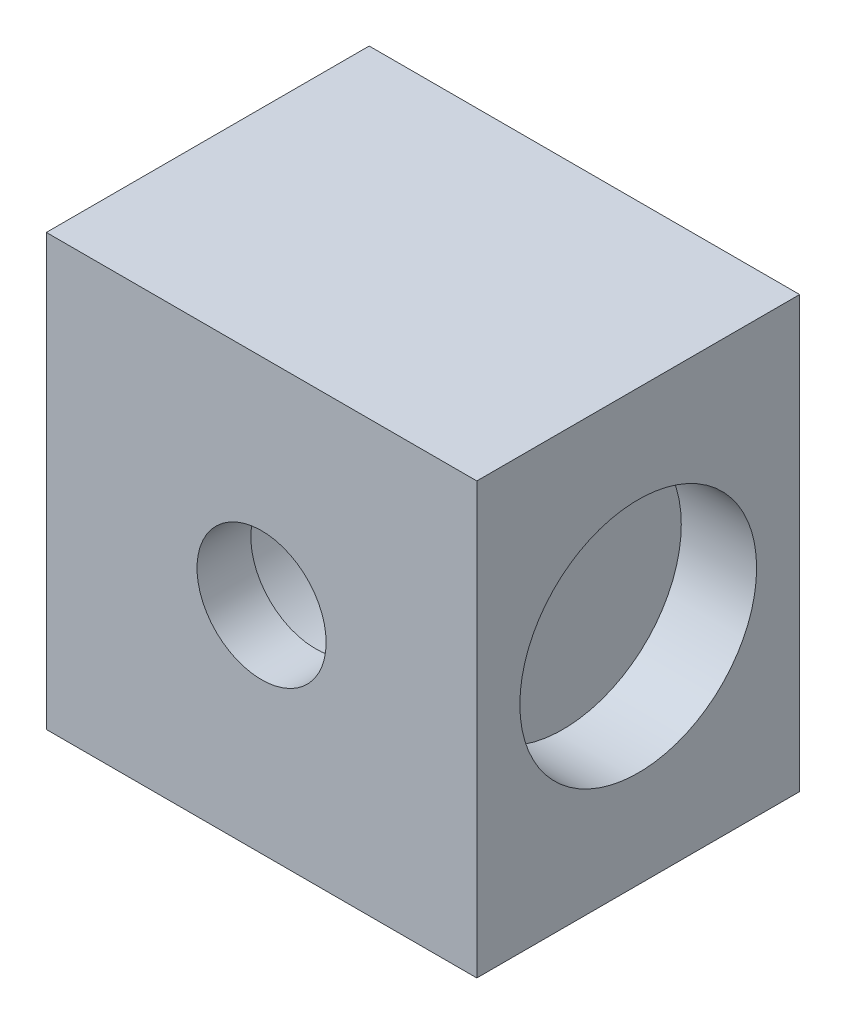
SolidWorks part; units mm, degrees
ref_plane "Front Plane" through (0, 0, 0) normal (0, 0, 1) x (1, 0, 0)
ref_plane "Top Plane" through (0, 0, 0) normal (0, 1, 0) x (1, 0, 0)
ref_plane "Right Plane" through (0, 0, 0) normal (1, 0, 0) x (0, 0, -1)
sketch "Sketch2" plane through (0, 0, 0) normal (0, 0, 1) x (1, 0, 0)
  line L1 (20, -20) -> (-20, -20)
  line L2 (20, -20) -> (20, 20)
  line L3 (20, 20) -> (-20, 20)
  line L4 (-20, -20) -> (-20, 20)
  line L5 (20, -20) -> (-20, 20) construction
  line L6 (20, 20) -> (-20, -20) construction
  point P0 (0, 0)
  dimension "D1" = 40
  dimension "D2" = 40
extrude "Boss-Extrude1" add sketch "Sketch2" along normal blind 30
sketch "Sketch3" plane through (0, 0, 30) normal (0, 0, 1) x (1, 0, 0)
  circle A0 centre (0, 0) radius 6
  dimension "D1" = 12
sketch "Sketch4" plane through (0, 0, 0) normal (0, 0, -1) x (-1, 0, 0)
  circle A0 centre (0, 0) radius 10
  dimension "D1" = 20
ref_plane "Plane1" through (20, 0, 0) normal (1, 0, 0) x (0, 0, -1)
sketch "Sketch6" plane through (20, 0, 0) normal (1, 0, 0) x (0, 0, -1)
  line L1 (-28, 13) -> (-2, 13)
  line L2 (-28, 13) -> (-28, -13)
  line L3 (-28, -13) -> (-2, -13)
  line L4 (-2, 13) -> (-2, -13)
  dimension "D1" = 26
  dimension "D2" = 26
  dimension "D3" = 13
  dimension "D4" = 2
extrude "Boss-Extrude2" add sketch "Sketch6" against normal up to next (40 mm away)
sketch "Sketch7" plane through (20, 0, 0) normal (1, 0, 0) x (0, 0, -1)
  line L2 (-30, -20) -> (-30, 20) construction
  line L3 (-30, 20) -> (0, 20) construction
  circle A0 centre (-15, 0) radius 11
  point P2 (0, 0)
  point P5 (-30, 0)
  point P6 (0, 0)
  point P9 (-15, 20)
  point P10 (0, 0)
  point P11 (-15, 0)
  point P12 (0, 0)
  dimension "D1" = 22
extrude "Cut-Extrude3" cut sketch "Sketch7" against normal blind 7
extrude "Cut-Extrude4" cut sketch "Sketch3" against normal blind 5
extrude "Cut-Extrude5" cut sketch "Sketch4" against normal blind 25
